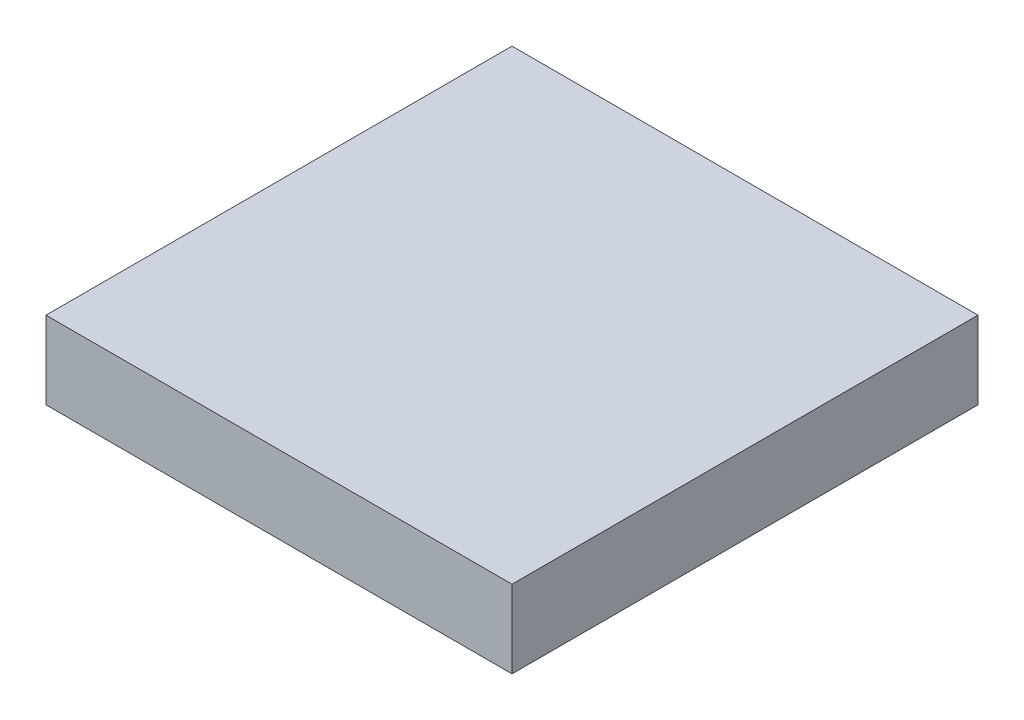
SolidWorks part; units mm, degrees
ref_plane "Front Plane" through (0, 0, 0) normal (0, 0, 1) x (1, 0, 0)
ref_plane "Top Plane" through (0, 0, 0) normal (0, 1, 0) x (1, 0, 0)
ref_plane "Right Plane" through (0, 0, 0) normal (1, 0, 0) x (0, 0, -1)
sketch "Sketch2" plane through (0, 0, 0) normal (0, 1, 0) x (1, 0, 0)
  line L1 (-15, 15) -> (15, 15)
  line L2 (-15, 15) -> (-15, -15)
  line L3 (-15, -15) -> (15, -15)
  line L4 (15, 15) -> (15, -15)
  line L5 (-15, 15) -> (15, -15) construction
  line L6 (-15, -15) -> (15, 15) construction
  point P0 (0, 0)
  dimension "D1" = 30
  dimension "D2" = 30
extrude "Boss-Extrude1" add sketch "Sketch2" along normal blind 5
